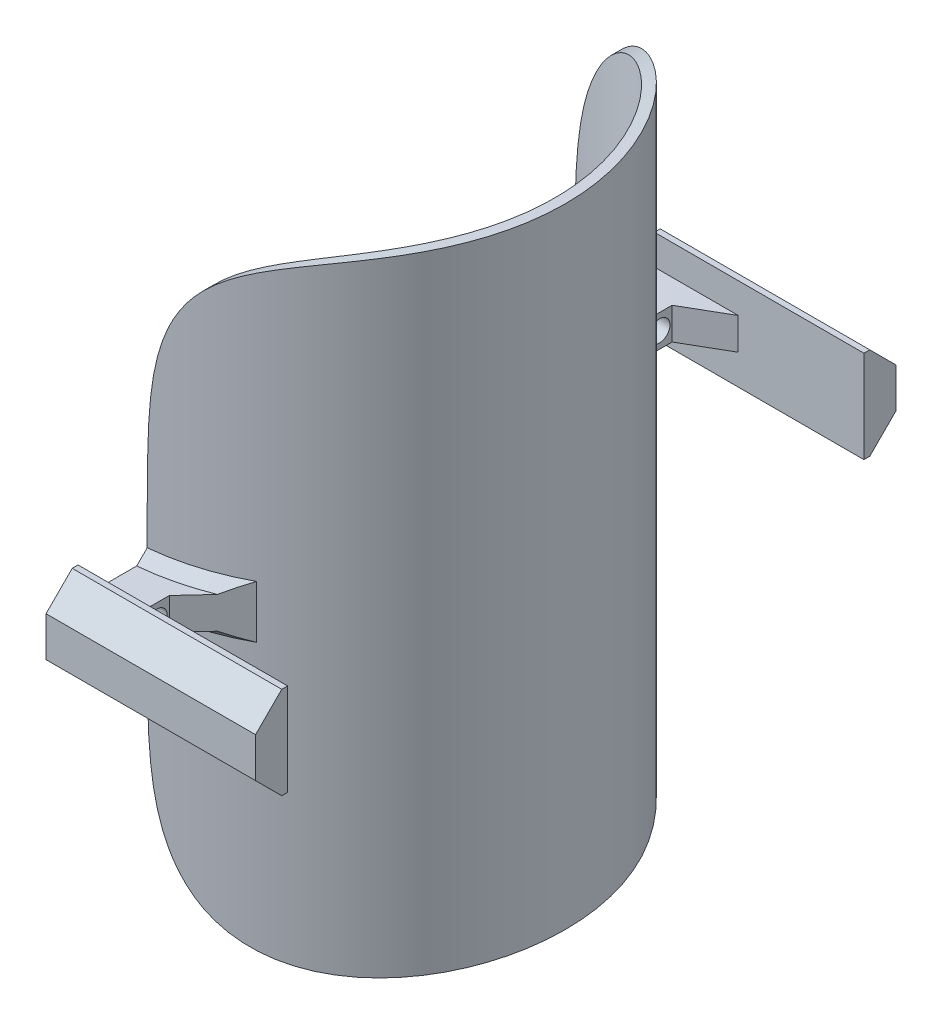
SolidWorks part; units mm, degrees
ref_plane "Ebene vorne" through (0, 0, 0) normal (0, 0, 1) x (1, 0, 0)
ref_plane "Ebene oben" through (0, 0, 0) normal (0, 1, 0) x (1, 0, 0)
ref_plane "Ebene rechts" through (0, 0, 0) normal (1, 0, 0) x (0, 0, -1)
sketch "Sketch2" plane through (0, 0, 0) normal (0, 1, 0) x (1, 0, 0)
  circle A0 centre (0, 0) radius 50
  dimension "D1" = 100
extrude "Extrude-Thin1" add sketch "Sketch2" along normal mid plane 150 thin
sketch "Sketch3" plane through (0, 0, 0) normal (0, 1, 0) x (1, 0, 0)
  line L0 (5, 59.3811) -> (5, -67.268)
  line L3 (5, 59.3811) -> (-132.8293, 10.5432)
  line L4 (-132.8293, 10.5432) -> (5, -67.268)
  dimension "D1" = 5
extrude "Cut-Extrude1" cut sketch "Sketch3" along normal mid plane 150
sketch "Sketch4" plane through (5, 0, 0) normal (-1, 0, 0) x (0, 0, 1)
  line L0 (0, 112.562) -> (0, -61.6099) construction
  line L1 (121.4294, 0) -> (-90.1078, 0) construction
  line L4 (76.4114, -4.75) -> (76.4114, 4.75)
  line L8 (76.4114, 4.75) -> (70.1614, 11)
  line L9 (70.1614, 11) -> (68.7614, 11)
  line L10 (68.7614, 11) -> (68.7614, 3.8)
  line L11 (68.7614, 3.8) -> (52.2614, 3.8)
  line L12 (52.2614, -75) -> (52.2614, 75) construction
  line L13 (68.7614, -3.8) -> (52.2614, -3.8)
  line L14 (68.7614, -11) -> (68.7614, -3.8)
  line L15 (70.1614, -11) -> (68.7614, -11)
  line L16 (76.4114, -4.75) -> (70.1614, -11)
  line L17 (68.7614, 3.8) -> (68.7614, -3.8)
  line L18 (52.2614, 3.8) -> (49.7494, 3.8)
  line L19 (49.7494, -75) -> (49.7494, 75) construction
  line L20 (49.7494, 3.8) -> (49.7494, -3.8)
  line L21 (49.7494, -3.8) -> (52.2614, -3.8)
  point P19 (76.4114, 0)
  dimension "D1" = 16.5
  dimension "D2" = 3.8
  dimension "D3" = 7.2
  dimension "D4" = 7.65
  dimension "D5" = 1.4
  dimension "D6" = 135
extrude "Boss-Extrude3" add sketch "Sketch4" against normal blind 10 contours L20 L21 L13 L17 L11 L18
sketch "Sketch8" plane through (5, 0, 0) normal (-1, 0, 0) x (0, 0, 1)
  line L0 (68.7614, 11) -> (68.7614, 3.8) construction
  line L1 (70.1614, 11) -> (68.7614, 11) construction
  line L2 (76.4114, 4.75) -> (70.1614, 11) construction
  line L3 (76.4114, -4.75) -> (76.4114, 4.75) construction
  line L4 (76.4114, -4.75) -> (70.1614, -11) construction
  line L5 (70.1614, -11) -> (68.7614, -11) construction
  line L6 (68.7614, -11) -> (68.7614, -3.8) construction
  line L7 (68.7614, 11) -> (68.7614, 3.8)
  line L8 (70.1614, 11) -> (68.7614, 11)
  line L9 (76.4114, 4.75) -> (70.1614, 11)
  line L10 (76.4114, -4.75) -> (76.4114, 4.75)
  line L11 (76.4114, -4.75) -> (70.1614, -11)
  line L12 (70.1614, -11) -> (68.7614, -11)
  line L13 (68.7614, -11) -> (68.7614, -3.8)
  line L14 (68.7614, 3.8) -> (68.7614, -3.8)
extrude "Boss-Extrude4" add sketch "Sketch8" against normal blind 50
chamfer "Chamfer1" distance 10 angle 30 1 edges at (15, 0, 68.7614)
sketch "Sketch9" plane through (15, 0, 0) normal (1, 0, 0) x (0, 0, -1)
  line L0 (-121.4294, 0) -> (90.1078, 0) construction
  line L1 (-62.9879, 3.8) -> (-62.9879, -3.8) construction
  circle A0 centre (-59.9879, 0) radius 2.5
  dimension "D1" = 5
  dimension "D2" = 3
extrude "Cut-Extrude2" cut sketch "Sketch9" against normal up to next
sketch "Sketch10" plane through (0, -3.8, 0) normal (0, -1, 0) x (1, 0, 0)
  line L0 (15, 56.9879) -> (25, 46.1655)
  line L1 (15, 50.3115) -> (15, 62.9879) construction
  line L4 (15, 50.3115) -> (15, 62.9879)
  line L5 (15, 62.9879) -> (25, 68.7614)
  line L6 (25, 68.7614) -> (5, 68.7614)
  line L7 (5, 68.7614) -> (5, 52.2614)
  line L8 (15, 50.3115) -> (15, 62.9879)
  line L9 (15, 62.9879) -> (25, 68.7614)
  line L10 (25, 68.7614) -> (5, 68.7614)
  line L11 (5, 68.7614) -> (5, 52.2614)
  arc A0 (5, -52.2614) -> (5, 52.2614) centre (0, 0) ccw construction
  arc A1 (15, 50.3115) -> (5, 52.2614) centre (0, 0) ccw
  arc A3 (5, -52.2614) -> (5, 52.2614) centre (0, 0) ccw
  arc A6 (15, 50.3115) -> (5, 52.2614) centre (0, 0) ccw
  line M7 (15, 50.3115) -> (15, 62.9879)
  dimension "D2" = 6
  dimension "D1" = 0
extrude "Boss-Extrude5" add sketch "Sketch10" against normal blind 7.6 contours A3 L0 M7
chamfer "Chamfer2" distance 2.5 angle 45 2 edges at (15.3065, -3.8, 50.2191) (15.3065, 3.8, 50.2191)
mirror "Mirror1" about plane through (0, 0, 0) normal (0, 0, 1) of "Chamfer2", "Boss-Extrude5", "Cut-Extrude2", "Chamfer1", "Boss-Extrude4", "Boss-Extrude3"
sketch "Sketch12" plane through (0, 0, 0) normal (0, 0, 1) x (1, 0, 0)
  line L12 (5, 6.3) -> (5, 75) construction
  line L13 (5, 32.7082) -> (5, 3.7987) construction
  line L16 (72.4491, 75) -> (32.5509, 75) construction
  line L17 (50, 75) -> (5, 75) construction
  line L18 (5, 15) -> (5, 75)
  line L19 (5, 75) -> (52.5, 75)
  spline S0 degree 3 poles (5, 15) (5, 32.5672) (5.6449, 59.4871) (26.9377, 75) (52.5, 75) knots 0 0 0 0 0.461851 1 1 1 1
  dimension "D1" = 60
  dimension "D2" = 20
  dimension "D3" = 5
extrude "Cut-Extrude4" cut sketch "Sketch12" against normal mid plane 110
mirror "Mirror4" about plane through (0, 0, 0) normal (0, 1, 0) of "Cut-Extrude4"
